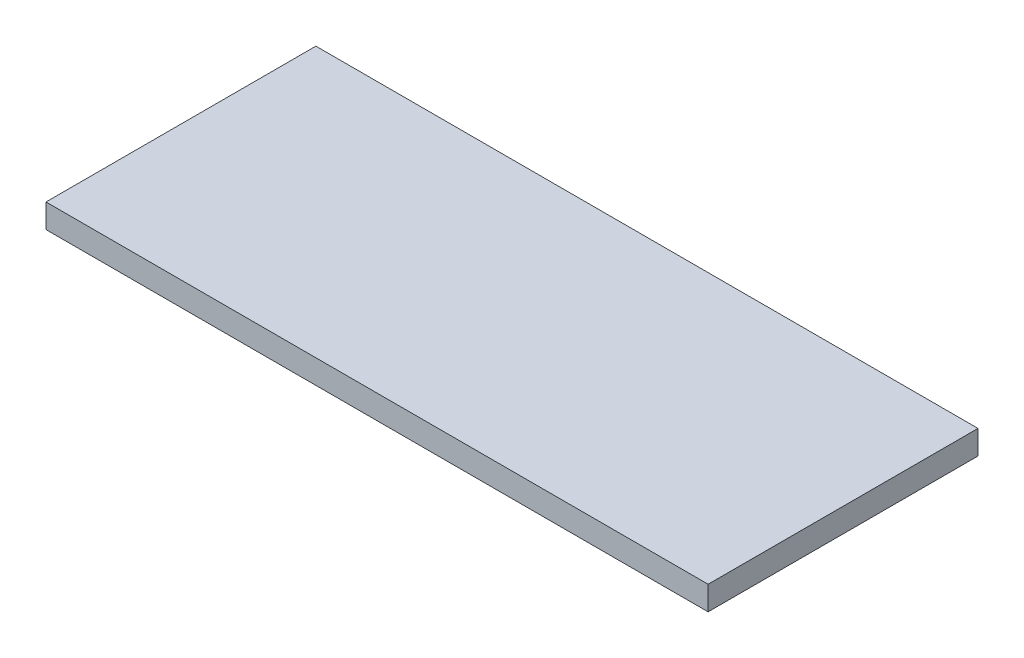
SolidWorks part; units mm, degrees
ref_plane "Спереди" through (0, 0, 0) normal (0, 0, 1) x (1, 0, 0)
ref_plane "Сверху" through (0, 0, 0) normal (0, 1, 0) x (1, 0, 0)
ref_plane "Справа" through (0, 0, 0) normal (1, 0, 0) x (0, 0, -1)
sketch "Эскиз1" plane through (0, 0, 0) normal (0, 1, 0) x (1, 0, 0)
  line L1 (249, -101.5) -> (-249, -101.5)
  line L2 (249, -101.5) -> (249, 101.5)
  line L3 (249, 101.5) -> (-249, 101.5)
  line L4 (-249, -101.5) -> (-249, 101.5)
  line L5 (249, -101.5) -> (-249, 101.5) construction
  line L6 (249, 101.5) -> (-249, -101.5) construction
  point P0 (0, 0)
  dimension "D1" = 498
  dimension "D2" = 203
extrude "Бобышка-Вытянуть1" add sketch "Эскиз1" along normal blind 18
